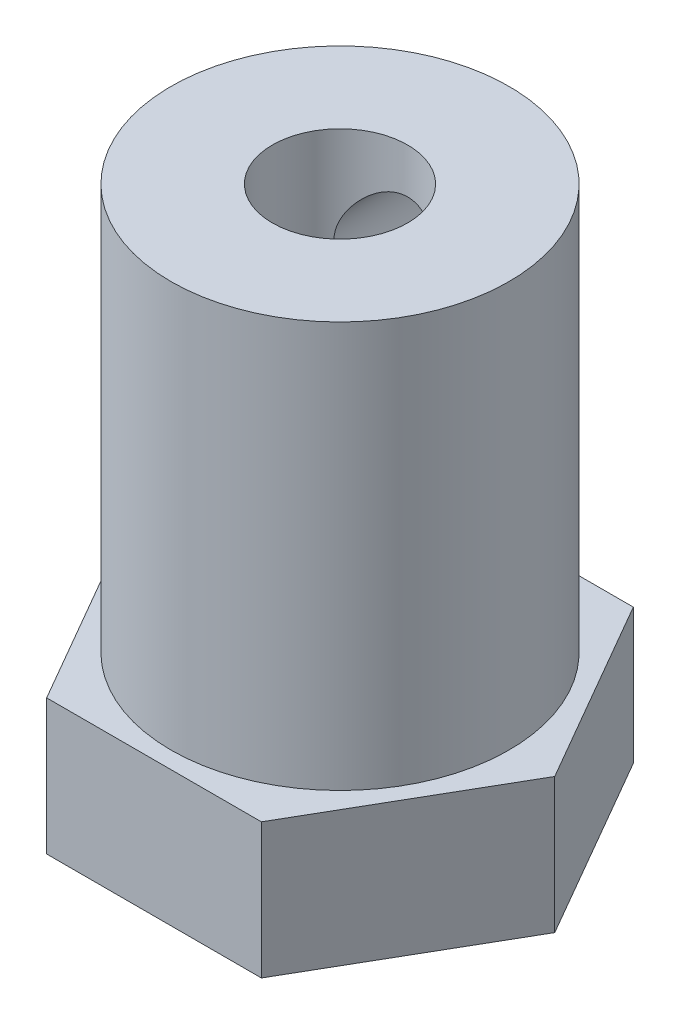
SolidWorks part; units mm, degrees
ref_plane "Front Plane" through (0, 0, 0) normal (0, 0, 1) x (1, 0, 0)
ref_plane "Top Plane" through (0, 0, 0) normal (0, 1, 0) x (1, 0, 0)
ref_plane "Right Plane" through (0, 0, 0) normal (1, 0, 0) x (0, 0, -1)
sketch "Sketch1" plane through (0, 0, 0) normal (0, 1, 0) x (1, 0, 0)
  line L1 (6.3509, 0) -> (3.1754, 5.5)
  line L2 (3.1754, 5.5) -> (-3.1754, 5.5)
  line L3 (-3.1754, 5.5) -> (-6.3509, 0)
  line L4 (-6.3509, 0) -> (-3.1754, -5.5)
  line L5 (-3.1754, -5.5) -> (3.1754, -5.5)
  line L6 (3.1754, -5.5) -> (6.3509, 0)
  circle A0 centre (0, 0) radius 5.5 construction
  dimension "D1" = 11
extrude "Boss-Extrude1" add sketch "Sketch1" along normal blind 4
sketch "Sketch2" plane through (0, 4, 0) normal (0, 1, 0) x (1, 0, 0)
  circle A0 centre (0, 0) radius 5
  dimension "D1" = 10
extrude "Boss-Extrude2" add sketch "Sketch2" along normal blind 12
sketch "Sketch3" plane through (0, 16, 0) normal (0, 1, 0) x (1, 0, 0)
  circle A0 centre (0, 0) radius 2
  dimension "D1" = 4
extrude "Cut-Extrude1" cut sketch "Sketch3" against normal through all and the other way through all
sketch "Sketch4" plane through (0, 0, 0) normal (0, 0, 1) x (1, 0, 0)
  line L0 (0, 16) -> (0, 0) construction
  line L1 (2, 16) -> (-2, 16) construction
  line L2 (-3.1754, 0) -> (3.1754, 0) construction
  circle A0 centre (0, 13.1698) radius 1.5
  dimension "D1" = 3
extrude "Cut-Extrude2" cut sketch "Sketch4" against normal blind 12
